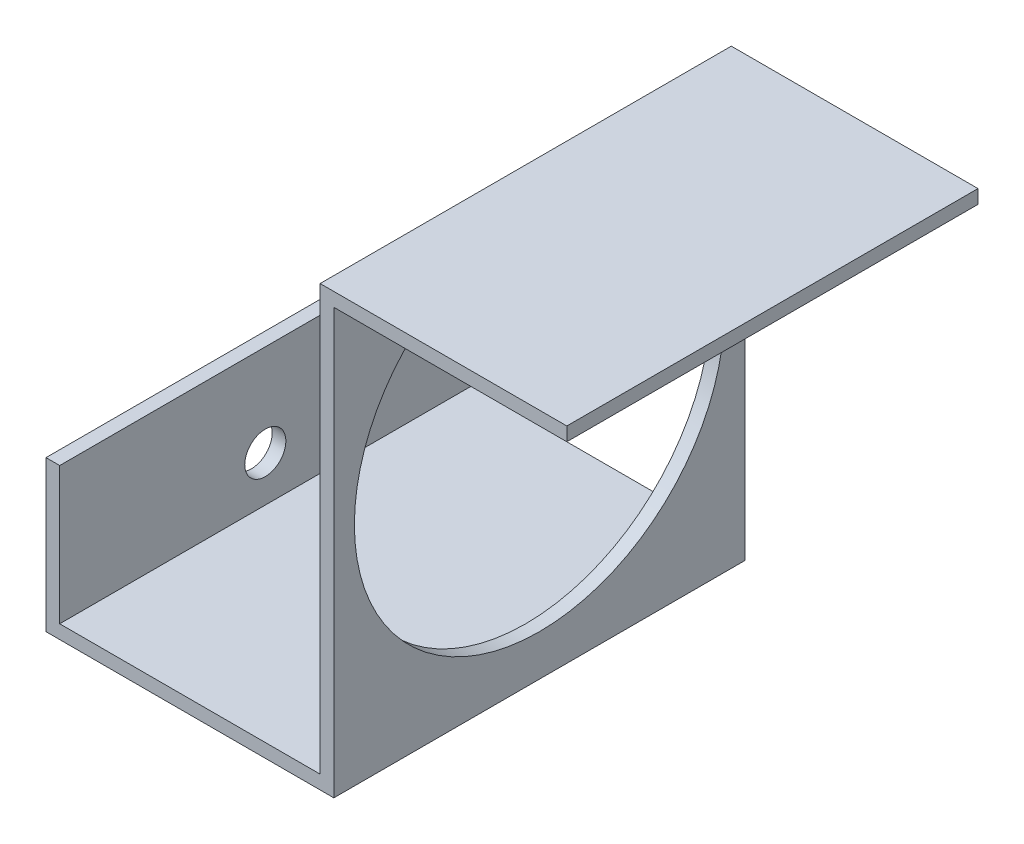
SolidWorks part; units mm, degrees
ref_plane "前视基准面" through (0, 0, 0) normal (0, 0, 1) x (1, 0, 0)
ref_plane "上视基准面" through (0, 0, 0) normal (0, 1, 0) x (1, 0, 0)
ref_plane "右视基准面" through (0, 0, 0) normal (1, 0, 0) x (0, 0, -1)
sketch "草图1" plane through (0, 0, 0) normal (0, 0, 1) x (1, 0, 0)
  line L0 (-21.1673, 37.6728) -> (-21.1673, 27.6728)
  line L1 (-21.1673, 27.6728) -> (-2.1673, 27.6728)
  line L4 (-22.1673, 26.6728) -> (-22.1673, 37.6728)
  line L5 (-22.1673, 37.6728) -> (-21.1673, 37.6728)
  line L6 (-21.1673, 27.6728) -> (-2.1673, 27.6728) construction
  line L8 (-1.1673, 57.6728) -> (15.8327, 57.6728)
  line L9 (15.8327, 57.6728) -> (15.8327, 58.6728)
  line L10 (15.8327, 58.6728) -> (-2.1673, 58.6728)
  line L11 (-2.1673, 58.6728) -> (-2.1673, 27.6728)
  line L13 (-1.1673, 57.6728) -> (-1.1673, 26.6728)
  line L14 (-1.1673, 26.6728) -> (-22.1673, 26.6728)
extrude "凸台-拉伸1" add sketch "草图1" along normal blind 30
sketch "草图4" plane through (-22.1673, 0, 0) normal (-1, 0, 0) x (0, 0, 1)
  line L0 (15, 26.6728) -> (15, 30.9728) construction
  line L1 (30, 26.6728) -> (0, 26.6728) construction
  circle A0 centre (15, 30.9728) radius 1.5
extrude "切除-拉伸3" cut sketch "草图4" against normal blind 2
sketch "草图5" plane through (-2.1673, 0, 0) normal (-1, 0, 0) x (0, 0, 1)
  line L0 (15, 58.6728) -> (15, 27.6728) construction
  line L1 (30, 58.6728) -> (0, 58.6728) construction
  line L2 (30, 27.6728) -> (0, 27.6728) construction
  circle A0 centre (15, 43.1728) radius 13.5
extrude "切除-拉伸4" cut sketch "草图5" against normal blind 5
